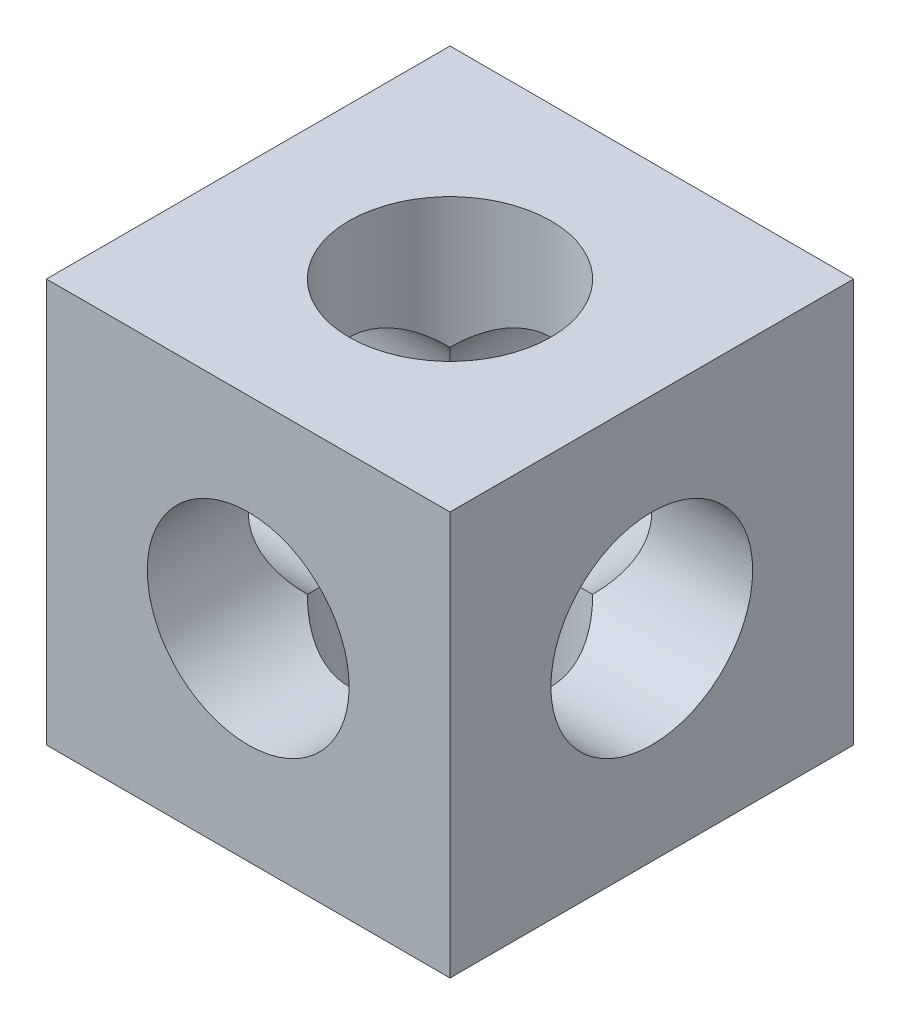
SolidWorks part; units mm, degrees
ref_plane "Front Plane" through (0, 0, 0) normal (0, 0, 1) x (1, 0, 0)
ref_plane "Top Plane" through (0, 0, 0) normal (0, 1, 0) x (1, 0, 0)
ref_plane "Right Plane" through (0, 0, 0) normal (1, 0, 0) x (0, 0, -1)
sketch "Sketch1" plane through (0, 0, 0) normal (0, 0, 1) x (1, 0, 0)
  line L1 (0, 0) -> (50.8, 0)
  line L2 (0, 0) -> (0, 50.8)
  line L3 (0, 50.8) -> (50.8, 50.8)
  line L4 (50.8, 0) -> (50.8, 50.8)
  dimension "D1" = 50.8
  dimension "D2" = 50.8
extrude "Boss-Extrude1" add sketch "Sketch1" along normal blind 50.8
sketch "Sketch2" plane through (0, 0, 50.8) normal (0, 0, 1) x (1, 0, 0)
  line L0 (0, 50.8) -> (0, 0) construction
  line L1 (50.8, 50.8) -> (0, 50.8) construction
  circle A0 centre (25.4, 25.4) radius 12.7
  dimension "D1" = 25.4
  dimension "D2" = 25.4
  dimension "D3" = 25.4
extrude "Cut-Extrude1" cut sketch "Sketch2" against normal blind 50.8
sketch "Sketch3" plane through (0, 50.8, 0) normal (0, 1, 0) x (1, 0, 0)
  line L0 (50.8, 0) -> (0, 0) construction
  line L2 (0, -50.8) -> (0, 0) construction
  circle A0 centre (25.4, -25.4) radius 12.7
  dimension "D1" = 25.4
  dimension "D2" = 25.4
  dimension "D3" = 25.4
extrude "Cut-Extrude2" cut sketch "Sketch3" against normal blind 50.8
sketch "Sketch4" plane through (0, 0, 0) normal (-1, 0, 0) x (0, 0, 1)
  line L0 (0, 50.8) -> (0, 0) construction
  line L1 (50.8, 0) -> (0, 0) construction
  circle A0 centre (25.4, 25.4) radius 12.7
  dimension "D1" = 25.4
  dimension "D2" = 25.4
  dimension "D3" = 25.4
extrude "Cut-Extrude3" cut sketch "Sketch4" against normal blind 50.8
